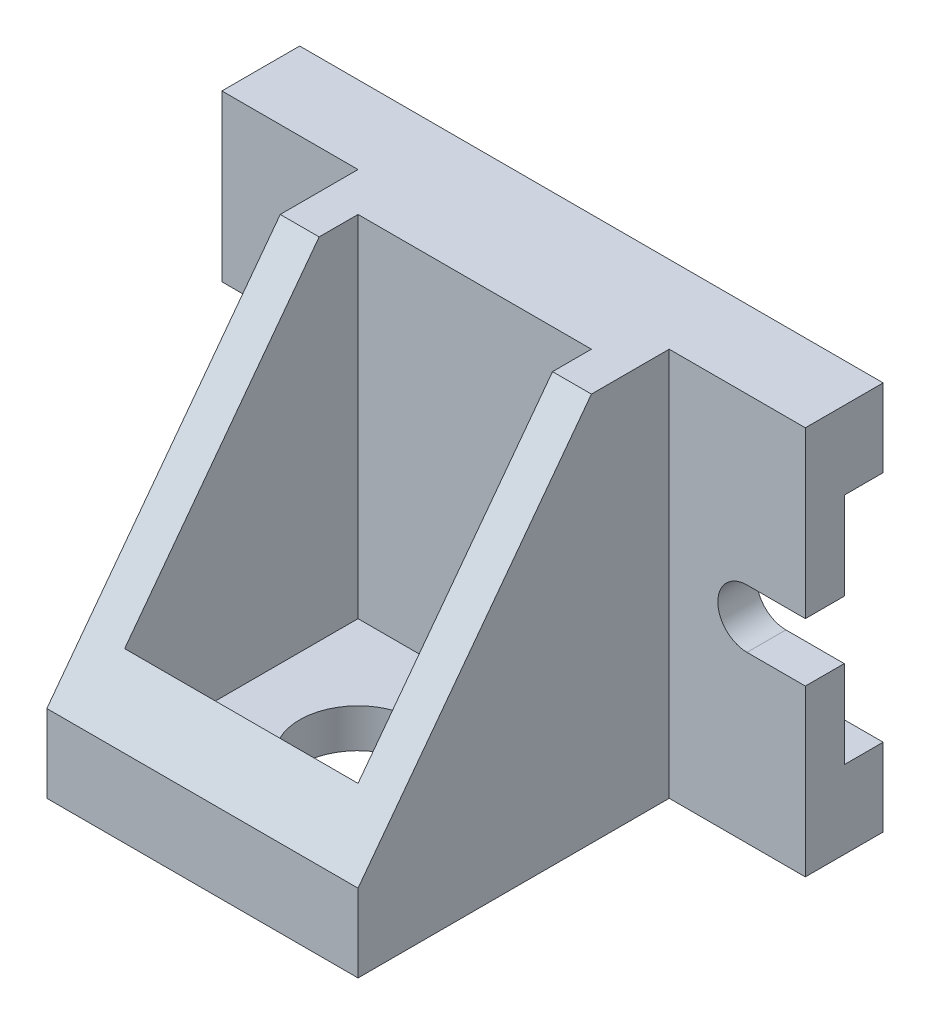
SolidWorks part; units mm, degrees
ref_plane "Alzado" through (0, 0, 0) normal (0, 0, 1) x (1, 0, 0)
ref_plane "Planta" through (0, 0, 0) normal (0, 1, 0) x (1, 0, 0)
ref_plane "Vista lateral" through (0, 0, 0) normal (1, 0, 0) x (0, 0, -1)
sketch "Croquis2" plane through (0, 0, 0) normal (0, 0, 1) x (1, 0, 0)
  line L0 (0, 74.65) -> (0, -91.4572) construction
  line L1 (-75, 50) -> (75, 50)
  line L2 (-75, 50) -> (-75, 7.5)
  line L3 (-75, -50) -> (75, -50)
  line L4 (75, 50) -> (75, 7.5)
  line L5 (-75, 50) -> (75, -50) construction
  line L6 (-75, -50) -> (75, 50) construction
  line L7 (-60, 7.5) -> (-75, 7.5)
  line L8 (-60, -7.5) -> (-75, -7.5)
  line L9 (60, -7.5) -> (75, -7.5)
  line L10 (60, 7.5) -> (75, 7.5)
  line L11 (-75, -7.5) -> (-75, -50)
  line L12 (75, -7.5) -> (75, -50)
  arc A0 (-60, -7.5) -> (-60, 7.5) centre (-60, 0) ccw
  arc A1 (60, -7.5) -> (60, 7.5) centre (60, 0) cw
  point P0 (0, 0)
  dimension "D3" = 15
  dimension "D1" = 150
  dimension "D2" = 100
  dimension "D4" = 15
  dimension "D5" = 50
extrude "Saliente-Extruir1" add sketch "Croquis2" along normal blind 20
sketch "Croquis3" plane through (-75, 0, 0) normal (-1, 0, 0) x (0, 0, 1)
  line L1 (0, 30) -> (10, 30)
  line L2 (0, 30) -> (0, -30)
  line L3 (0, -30) -> (10, -30)
  line L4 (10, 30) -> (10, -30)
  line L9 (0, 50) -> (0, 7.5) construction
  dimension "D1" = 10
  dimension "D2" = 60
  dimension "D3" = 0
extrude "Cortar-Extruir1" cut sketch "Croquis3" against normal through all both and the other way through all
sketch "Croquis5" plane through (75, 0, 0) normal (1, 0, 0) x (0, 0, -1)
  line L1 (-40, 50) -> (-20, 50)
  line L3 (-40, -50) -> (-20, -50)
  line L4 (-20, 50) -> (-20, -50)
  line L8 (-40, -50) -> (-100, -50)
  line L9 (-100, -50) -> (-100, -30)
  line L10 (-100, -30) -> (-40, 50)
  line L11 (0, -50) -> (0, -30) construction
  point P0 (-30, 0)
  dimension "D2" = 100
  dimension "D3" = 20
  dimension "D4" = 100
extrude "Saliente-Extruir2" add sketch "Croquis5" against normal through all
sketch "Croquis6" plane through (75, 0, 0) normal (1, 0, 0) x (0, 0, -1)
  line L1 (-20, 50) -> (-100, 50)
  line L2 (-20, 50) -> (-20, -50)
  line L3 (-20, -50) -> (-100, -50)
  line L4 (-100, 50) -> (-100, -50)
  line L5 (-100, -50) -> (0, -50) construction
  line L6 (-40, 50) -> (0, 50) construction
  line L7 (-100, -30) -> (-100, -50) construction
  dimension "D1" = 0
  dimension "D2" = 80
  dimension "D3" = 0
extrude "Cortar-Extruir2" cut sketch "Croquis6" against normal blind 35 and the other way through all
sketch "Croquis7" plane through (-75, 0, 0) normal (-1, 0, 0) x (0, 0, 1)
  line L0 (40, 50) -> (0, 50) construction
  line L1 (20, 50) -> (100, 50)
  line L2 (20, 50) -> (20, -50)
  line L3 (20, -50) -> (100, -50)
  line L4 (100, 50) -> (100, -50)
  line L5 (100, -50) -> (0, -50) construction
  line L6 (20, -7.5) -> (20, 7.5) construction
  line L7 (100, -30) -> (100, -50) construction
  dimension "D1" = 0
  dimension "D2" = 0
extrude "Cortar-Extruir3" cut sketch "Croquis7" against normal blind 35
sketch "Croquis8" plane through (0, 50, 0) normal (0, 1, 0) x (1, 0, 0)
  line L0 (75, 0) -> (-75, 0) construction
  line L1 (-30, -30) -> (30, -30)
  line L2 (-30, -30) -> (-30, -90)
  line L3 (-30, -90) -> (30, -90)
  line L4 (30, -30) -> (30, -90)
  line L5 (40, -40) -> (40, -100) construction
  dimension "D1" = 30
  dimension "D2" = 60
  dimension "D3" = 60
  dimension "D4" = 10
extrude "Cortar-Extruir4" cut sketch "Croquis8" against normal blind 90
sketch "Croquis9" plane through (0, 50, 0) normal (0, 1, 0) x (1, 0, 0)
  line L0 (75, 0) -> (-75, 0) construction
  line L2 (-40, -40) -> (-40, -100) construction
  circle A0 centre (0, -60) radius 15
  dimension "D1" = 30
  dimension "D2" = 60
  dimension "D3" = 40
extrude "Cortar-Extruir5" cut sketch "Croquis9" against normal through all
